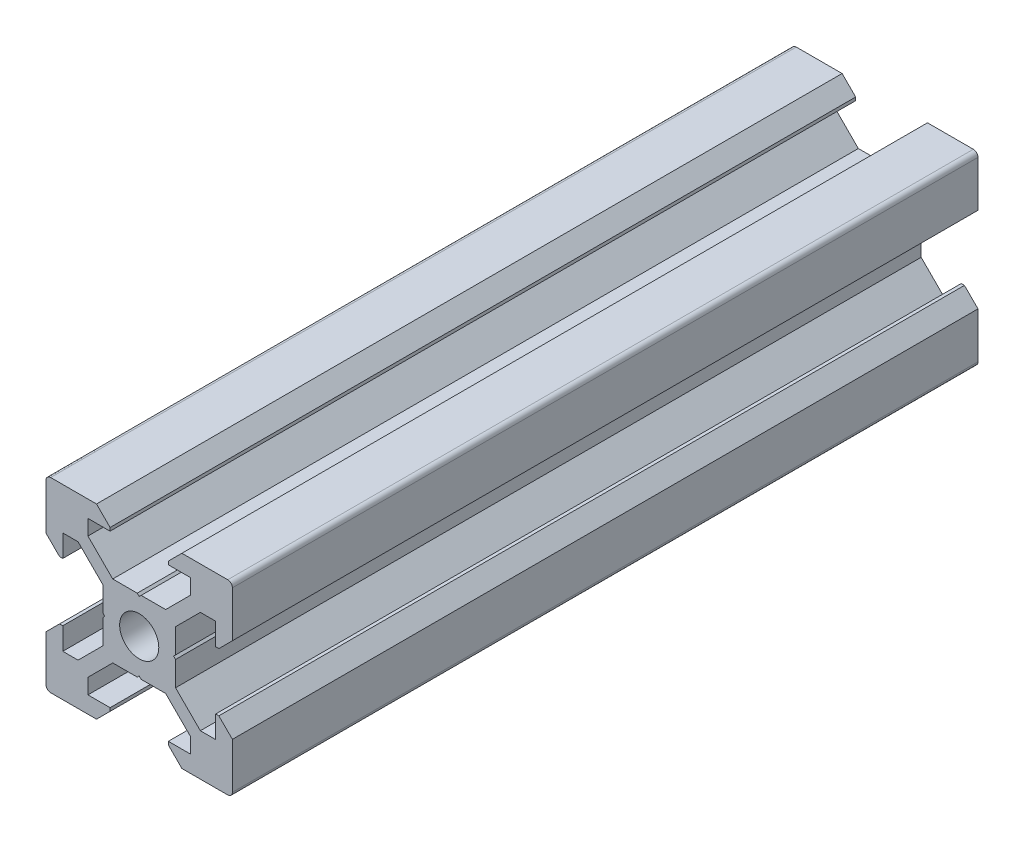
SolidWorks part; units mm, degrees
material "6061-T6 (SS)"
ref_plane "Front Plane" through (0, 0, 0) normal (0, 0, 1) x (1, 0, 0)
ref_plane "Top Plane" through (0, 0, 0) normal (0, 1, 0) x (1, 0, 0)
ref_plane "Right Plane" through (0, 0, 0) normal (1, 0, 0) x (0, 0, -1)
sketch "Sketch1" plane through (0, 0, 0) normal (0, 0, 1) x (1, 0, 0)
  line L1 (9.5, -10) -> (-9.5, -10)
  line L2 (10, -9.5) -> (10, 9.5)
  line L3 (9.5, 10) -> (-9.5, 10)
  line L4 (-10, -9.5) -> (-10, 9.5)
  line L5 (10, -10) -> (-10, 10) construction
  line L6 (10, 10) -> (-10, -10) construction
  circle A0 centre (0, 0) radius 2.1
  arc A1 (-9.5, 10) -> (-10, 9.5) centre (-9.5, 9.5) ccw
  arc A2 (10, 9.5) -> (9.5, 10) centre (9.5, 9.5) ccw
  arc A3 (9.5, -10) -> (10, -9.5) centre (9.5, -9.5) ccw
  arc A4 (-9.5, -10) -> (-10, -9.5) centre (-9.5, -9.5) cw
  point P0 (0, 0)
  line B0 (0, 0) -> (0, 10) construction
  line B1 (0, 3.69) -> (-0.21, 3.9)
  line B2 (-0.21, 3.9) -> (-2.8393, 3.9)
  line B3 (-2.8393, 3.9) -> (-5.5, 6.5607)
  line B4 (-5.5, 6.5607) -> (-5.5, 8.2)
  line B5 (-5.5, 8.2) -> (-3.125, 8.2)
  line B6 (-3.125, 8.2) -> (-3.125, 8.545)
  line B7 (-3.125, 8.545) -> (-4.58, 10)
  line B8 (-4.58, 10) -> (4.58, 10)
  line B9 (0, 0) -> (-5.9132, 5.9132) construction
  line B10 (3.125, 8.545) -> (4.58, 10)
  line B11 (3.125, 8.2) -> (3.125, 8.545)
  line B12 (5.5, 8.2) -> (3.125, 8.2)
  line B13 (5.5, 6.5607) -> (5.5, 8.2)
  line B14 (2.8393, 3.9) -> (5.5, 6.5607)
  line B15 (0.21, 3.9) -> (2.8393, 3.9)
  line B16 (0, 3.69) -> (0.21, 3.9)
  line B17 (0, 0) -> (-10, 0) construction
  line B18 (-3.69, 0) -> (-3.9, -0.21)
  line B19 (-3.9, -0.21) -> (-3.9, -2.8393)
  line B20 (-3.9, -2.8393) -> (-6.5607, -5.5)
  line B21 (-6.5607, -5.5) -> (-8.2, -5.5)
  line B22 (-8.2, -5.5) -> (-8.2, -3.125)
  line B23 (-8.2, -3.125) -> (-8.545, -3.125)
  line B24 (-8.545, -3.125) -> (-10, -4.58)
  line B25 (-10, -4.58) -> (-10, 4.58)
  line B26 (0, 0) -> (-5.9132, -5.9132) construction
  line B27 (-8.545, 3.125) -> (-10, 4.58)
  line B28 (-8.2, 3.125) -> (-8.545, 3.125)
  line B29 (-8.2, 5.5) -> (-8.2, 3.125)
  line B30 (-6.5607, 5.5) -> (-8.2, 5.5)
  line B31 (-3.9, 2.8393) -> (-6.5607, 5.5)
  line B32 (-3.9, 0.21) -> (-3.9, 2.8393)
  line B33 (-3.69, 0) -> (-3.9, 0.21)
  line B34 (0, 0) -> (0, -10) construction
  line B35 (0, -3.69) -> (0.21, -3.9)
  line B36 (0.21, -3.9) -> (2.8393, -3.9)
  line B37 (2.8393, -3.9) -> (5.5, -6.5607)
  line B38 (5.5, -6.5607) -> (5.5, -8.2)
  line B39 (5.5, -8.2) -> (3.125, -8.2)
  line B40 (3.125, -8.2) -> (3.125, -8.545)
  line B41 (3.125, -8.545) -> (4.58, -10)
  line B42 (4.58, -10) -> (-4.58, -10)
  line B43 (0, 0) -> (5.9132, -5.9132) construction
  line B44 (-3.125, -8.545) -> (-4.58, -10)
  line B45 (-3.125, -8.2) -> (-3.125, -8.545)
  line B46 (-5.5, -8.2) -> (-3.125, -8.2)
  line B47 (-5.5, -6.5607) -> (-5.5, -8.2)
  line B48 (-2.8393, -3.9) -> (-5.5, -6.5607)
  line B49 (-0.21, -3.9) -> (-2.8393, -3.9)
  line B50 (0, -3.69) -> (-0.21, -3.9)
  line B51 (0, 0) -> (10, 0) construction
  line B52 (3.69, 0) -> (3.9, 0.21)
  line B53 (3.9, 0.21) -> (3.9, 2.8393)
  line B54 (3.9, 2.8393) -> (6.5607, 5.5)
  line B55 (6.5607, 5.5) -> (8.2, 5.5)
  line B56 (8.2, 5.5) -> (8.2, 3.125)
  line B57 (8.2, 3.125) -> (8.545, 3.125)
  line B58 (8.545, 3.125) -> (10, 4.58)
  line B59 (10, 4.58) -> (10, -4.58)
  line B60 (0, 0) -> (5.9132, 5.9132) construction
  line B61 (8.545, -3.125) -> (10, -4.58)
  line B62 (8.2, -3.125) -> (8.545, -3.125)
  line B63 (8.2, -5.5) -> (8.2, -3.125)
  line B64 (6.5607, -5.5) -> (8.2, -5.5)
  line B65 (3.9, -2.8393) -> (6.5607, -5.5)
  line B66 (3.9, -0.21) -> (3.9, -2.8393)
  line B67 (3.69, 0) -> (3.9, -0.21)
  dimension "D1" = 4.2
  dimension "D3" = 0.5
  dimension "D2" = 20
sketch_block_instance "V Slot 1-4"
sketch_block "V Slot 1" parameters "D1"=10, "D2"=11, "D3"=4.3, "D4"=1.8, "D5"=0.21, "D6"=45, "D7"=9.16, "D8"=1.5, "D9"=6.25
sketch_block_instance "V Slot 1-5"
sketch_block_instance "V Slot 1-6"
sketch_block_instance "V Slot 1-7"
extrude "Boss-Extrude1" add sketch "Sketch1" along normal blind 80 contours B67 B52 B53 B54 B55 B56 B57 B58 L2 A2 L3 B10 B11 B12 B13 B14 B15 B16 B1 B2 B3 B4 B5 B6 B7 A1 L4 B27 B28 B29 B30 B31 B32 B33 B18 B19 B20 B21 B22 B23 B24 A4 L1 B44 B45 B46 B47 B48 B49
